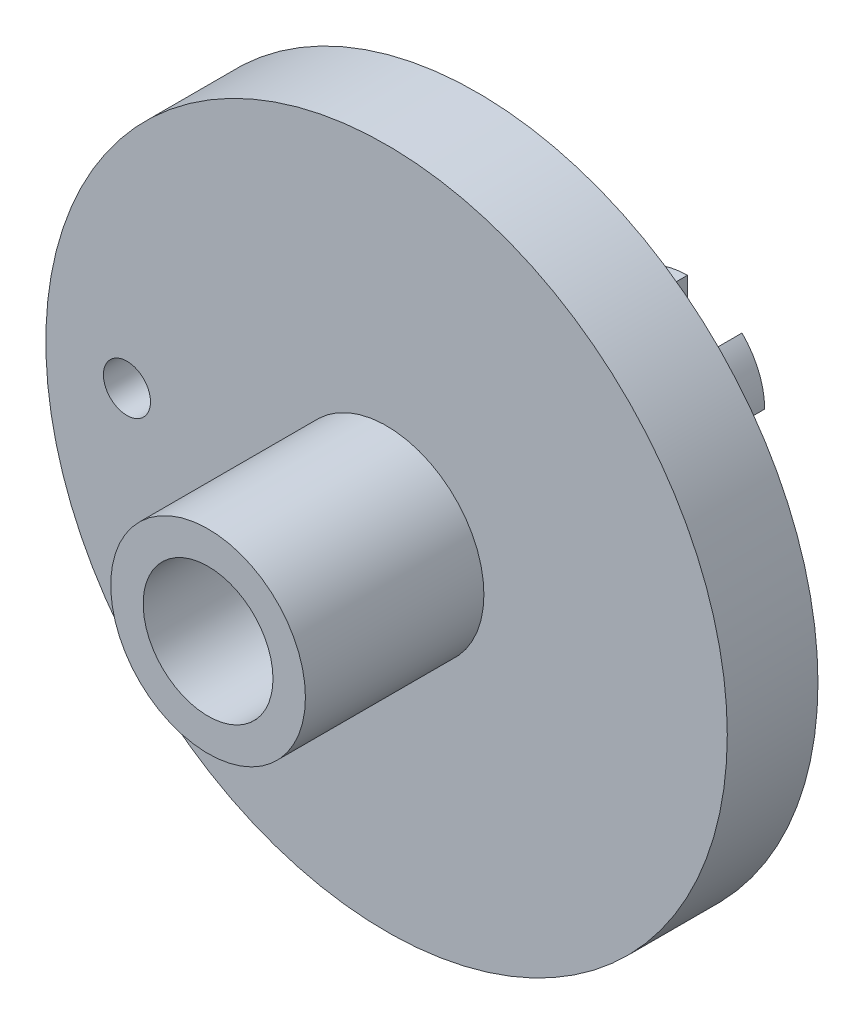
SolidWorks part; units mm, degrees
ref_plane "Front Plane" through (0, 0, 0) normal (0, 0, 1) x (1, 0, 0)
ref_plane "Top Plane" through (0, 0, 0) normal (0, 1, 0) x (1, 0, 0)
ref_plane "Right Plane" through (0, 0, 0) normal (1, 0, 0) x (0, 0, -1)
sketch "Sketch1" plane through (0, 0, 0) normal (0, 0, 1) x (1, 0, 0)
  circle A0 centre (0, 0) radius 4.7625
  dimension "D1" = 9.525
extrude "Boss-Extrude1" add sketch "Sketch1" against normal blind 16
sketch "Sketch2" plane through (0, 0, 0) normal (0, 0, 1) x (1, 0, 0)
  circle A0 centre (0, 0) radius 21
  dimension "D1" = 42
extrude "Boss-Extrude2" add sketch "Sketch2" against normal blind 5.588
sketch "Sketch3" plane through (0, 0, -16) normal (0, 0, -1) x (-1, 0, 0)
  line L0 (0, -4.7625) -> (0, 4.7625)
  line L1 (-4.7625, 0) -> (4.7625, 0)
  line L2 (3.3676, 3.3676) -> (-3.3676, -3.3676)
  line L3 (-3.3676, 3.3676) -> (3.3676, -3.3676)
  circle A0 centre (0, 0) radius 4.7625
  circle A1 centre (0, 0) radius 2.8
  circle M5 centre (0, 0) radius 4.7625
  dimension "D1" = 9.525
  dimension "D2" = 5.6
  dimension "D3" = 45
  dimension "D4" = 45
extrude "Boss-Extrude3" add sketch "Sketch3" along normal blind 2.54 contours A1 L3 L1 M5 | A1 L2 L0 M5 | A1 L3 L1 M5 | A1 L2 L0 M5
sketch "Sketch6" plane through (0, 0, 0) normal (0, 0, 1) x (1, 0, 0)
  circle A0 centre (0, 0) radius 1.55
  dimension "D1" = 3.1
extrude "Cut-Extrude1" cut sketch "Sketch6" against normal through all
sketch "Sketch7" plane through (0, 0, 0) normal (0, 0, 1) x (1, 0, 0)
  circle A0 centre (-16, 0) radius 1.45
  circle A2 centre (0, 0) radius 21 construction
  dimension "D1" = 2.9
  dimension "D2" = 16
extrude "Cut-Extrude2" cut sketch "Sketch7" against normal blind 7.62
sketch "Sketch8" plane through (0, 0, 0) normal (0, 0, 1) x (1, 0, 0)
  circle A0 centre (0, 0) radius 6
  circle A1 centre (0, 0) radius 4
  dimension "D1" = 12
  dimension "D2" = 8
extrude "Boss-Extrude4" add sketch "Sketch8" along normal blind 11
fillet "Fillet1" radius 2 1 edges at (4.7625, 0, -5.588)
